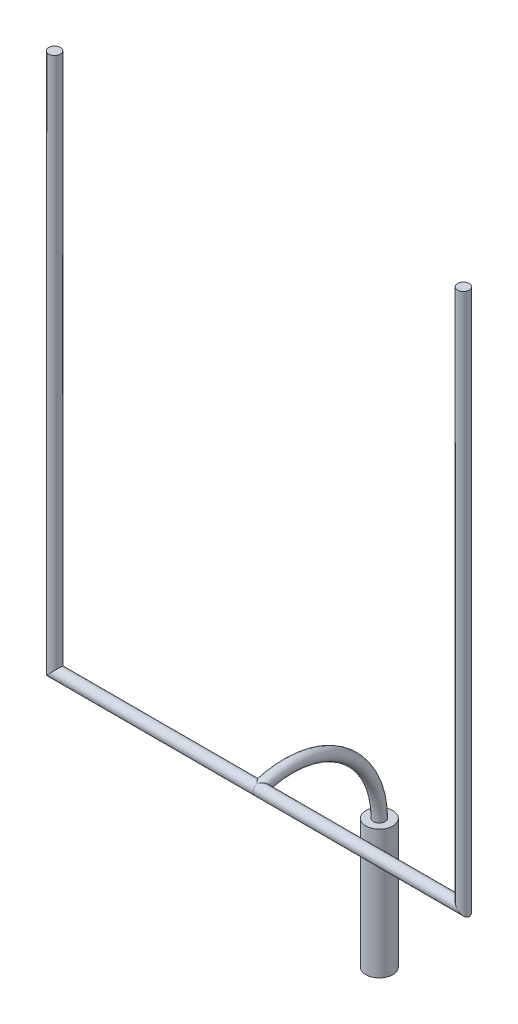
SolidWorks part; units mm, degrees
material "Alumina"
ref_plane "Front Plane" through (0, 0, 0) normal (0, 0, 1) x (1, 0, 0)
ref_plane "Top Plane" through (0, 0, 0) normal (0, 1, 0) x (1, 0, 0)
ref_plane "Right Plane" through (0, 0, 0) normal (1, 0, 0) x (0, 0, -1)
sketch "Sketch1" plane through (0, 0, 0) normal (0, 0, 1) x (1, 0, 0)
  line L1 (0, 0) -> (2901.95, 0)
  line L2 (2901.95, 0) -> (2901.95, 7620)
  line L3 (0, 0) -> (-2901.95, 0)
  line L4 (-2901.95, 0) -> (-2901.95, 7620)
  dimension "D1" = 5803.9
  dimension "D2" = 2901.95
  dimension "D3" = 7620
sketch "Sketch23" plane through (0, 0, 0) normal (1, 0, 0) x (0, 0, -1)
  line L0 (1708.15, -3048) -> (1708.15, -1219.2)
  arc A0 (1708.15, -1219.2) -> (0, 0) centre (418.9702, -1219.2) ccw
  dimension "D1" = 3048
  dimension "D2" = 1828.8
  dimension "D3" = 1708.15
sweep "Sweep4" add path "Sketch1" circular profile diameter 165.1 parameters "D3"=165.1
sweep "Sweep6" add path "Sketch23" circular profile diameter 165.1 parameters "D3"=165.1
sketch "Sketch69" plane through (0, -3048, 0) normal (0, -1, 0) x (1, 0, 0)
  circle A0 centre (0, -1708.15) radius 190.5
  dimension "D1" = 381
extrude "Boss-Extrude3" add sketch "Sketch69" against normal blind 1828.8 contours A0
sketch "Sketch70" plane through (0, -3048, 0) normal (0, -1, 0) x (1, 0, 0)
  line L0 (0, -1708.15) -> (0, 0) construction
  circle A0 centre (0, -1708.15) radius 190.5 construction
  point P0 (0, -1517.65)
  point P1 (0, -1898.65)
sketch "Sketch71" plane through (0, -3048, 0) normal (0, -1, 0) x (1, 0, 0)
  circle A0 centre (0, -1708.15) radius 190.5 construction
  point P0 (-190.5, -1708.15)
